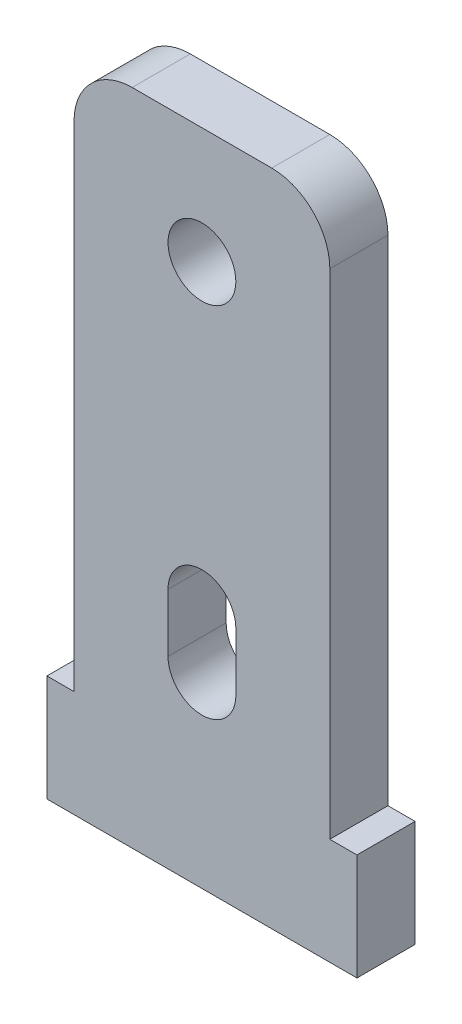
SolidWorks part; units mm, degrees
material "Custom Plastic"
ref_plane "Front Plane" through (0, 0, 0) normal (0, 0, 1) x (1, 0, 0)
ref_plane "Top Plane" through (0, 0, 0) normal (0, 1, 0) x (1, 0, 0)
ref_plane "Right Plane" through (0, 0, 0) normal (1, 0, 0) x (0, 0, -1)
sketch "Sketch1" plane through (0, 0, 0) normal (0, 0, 1) x (1, 0, 0)
  line L0 (0, -3) -> (0, -6) construction
  line L1 (-3.6, 18.5) -> (3.6, 18.5)
  line L2 (-6.6, 15.5) -> (-6.6, -15.5)
  line L3 (-6.6, -15.5) -> (6.6, -15.5)
  line L4 (6.6, 15.5) -> (6.6, -15.5)
  line L5 (-8, -10) -> (8, -10)
  line L6 (-8, -10) -> (-8, -15.5)
  line L7 (-8, -15.5) -> (8, -15.5)
  line L8 (8, -10) -> (8, -15.5)
  line L9 (1.75, -3) -> (1.75, -6)
  line L10 (-1.75, -3) -> (-1.75, -6)
  circle A0 centre (0, 12.5) radius 1.75
  arc A1 (1.75, -3) -> (-1.75, -3) centre (0, -3) ccw
  arc A2 (-1.75, -6) -> (1.75, -6) centre (0, -6) ccw
  arc A3 (3.6, 18.5) -> (6.6, 15.5) centre (3.6, 15.5) cw
  arc A4 (-3.6, 18.5) -> (-6.6, 15.5) centre (-3.6, 15.5) ccw
  point P8 (6.6, 0)
  point P10 (0, -15.5)
  point P11 (0, -15.5)
  point P12 (0, 18.5)
  point P17 (0, -4.5)
  point P24 (6.6, 18.5)
  point P27 (-6.6, 18.5)
  dimension "D5" = 3.5
  dimension "D6" = 1.75
  dimension "D10" = 3
  dimension "D1" = 34
  dimension "D2" = 5.5
  dimension "D3" = 13.2
  dimension "D4" = 16
  dimension "D7" = 17
  dimension "D8" = 4
  dimension "D9" = 3
extrude "Boss-Extrude1" add sketch "Sketch1" along normal blind 3 contours L2 L5 L4 L1 A2 L10 A1 L9 A0 | L5 L2 L3 L4 | L6 L7 L2 L5 | L8 L5 L4 L7
